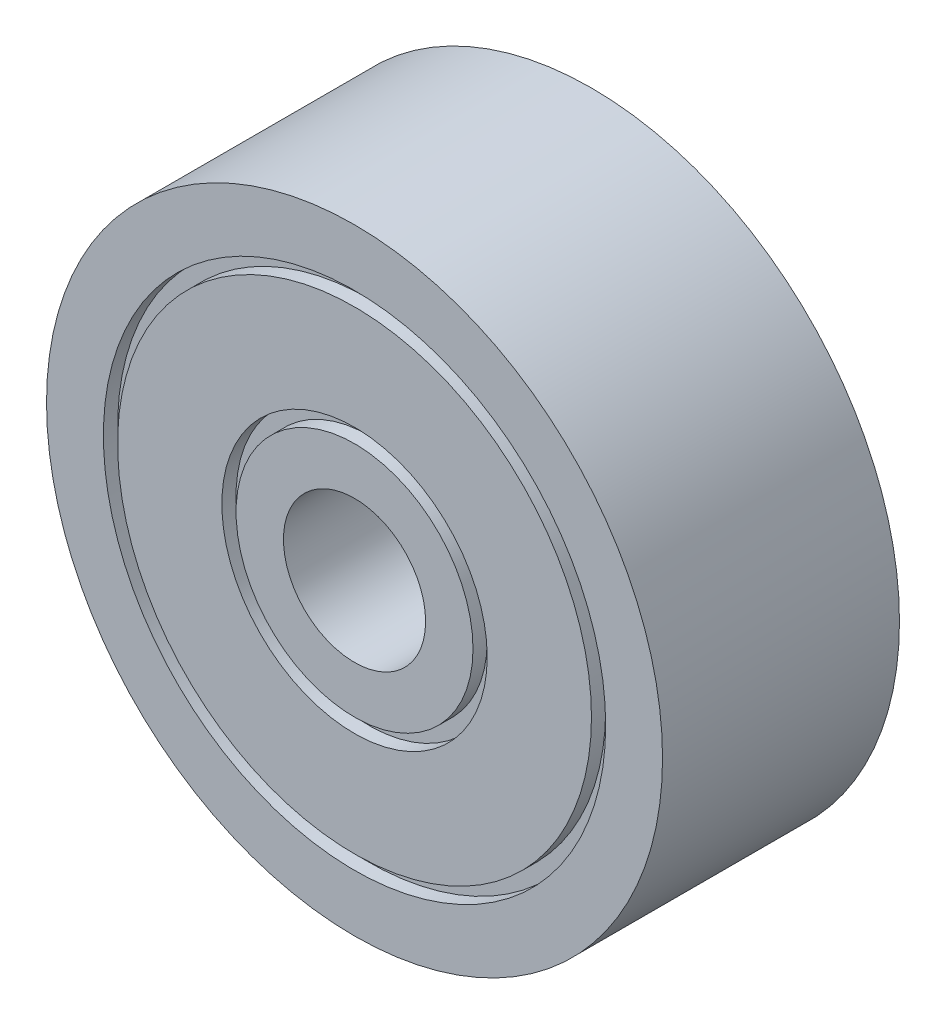
SolidWorks part; units mm, degrees
ref_plane "Front Plane" through (0, 0, 0) normal (0, 0, 1) x (1, 0, 0)
ref_plane "Top Plane" through (0, 0, 0) normal (0, 1, 0) x (1, 0, 0)
ref_plane "Right Plane" through (0, 0, 0) normal (1, 0, 0) x (0, 0, -1)
sketch "Esquisse1" plane through (0, 0, 0) normal (0, 0, 1) x (1, 0, 0)
  circle A0 centre (0, 0) radius 6.5
  circle A1 centre (0, 0) radius 1.5
  dimension "D1" = 13
  dimension "D2" = 3
extrude "Boss.-Extru.1" add sketch "Esquisse1" along normal blind 5
ref_axis "Axe1" through (0, 0, 5.25) along (0, 0, -1)
sketch "Esquisse3" plane through (0, 0, 0) normal (1, 0, 0) x (0, 0, -1)
  line L0 (-5, 6.5) -> (-5, -6.5) construction
  line L1 (-5, 2.8) -> (-4.7, 2.8)
  line L2 (-5, 2.8) -> (-5, 2.5)
  line L3 (-5, 2.5) -> (-4.7, 2.5)
  line L4 (-4.7, 2.8) -> (-4.7, 2.5)
  line L5 (2.75, 0) -> (-2.75, 0) construction
  line L6 (0, 7.15) -> (0, -7.15) construction
  line L7 (-0.3, 2.8) -> (0, 2.8)
  line L8 (-0.3, 2.8) -> (-0.3, 2.5)
  line L9 (-0.3, 2.5) -> (0, 2.5)
  line L10 (0, 2.8) -> (0, 2.5)
  line L12 (-4.7, 5) -> (-5, 5)
  line L13 (-4.7, 5) -> (-4.7, 5.3)
  line L14 (-4.7, 5.3) -> (-5, 5.3)
  line L15 (-5, 5) -> (-5, 5.3)
  line L16 (-0.3, 5) -> (0, 5)
  line L17 (-0.3, 5) -> (-0.3, 5.3)
  line L18 (-0.3, 5.3) -> (0, 5.3)
  line L19 (0, 5) -> (0, 5.3)
  dimension "D1" = 2.5
  dimension "D2" = 0.3
  dimension "D3" = 0.3
  dimension "D4" = 5
revolve "Enlèvement de matière-Révolution1" cut sketch "Esquisse3" angle 360 about axis through (0, 0, 5.25) along (0, 0, -1)
